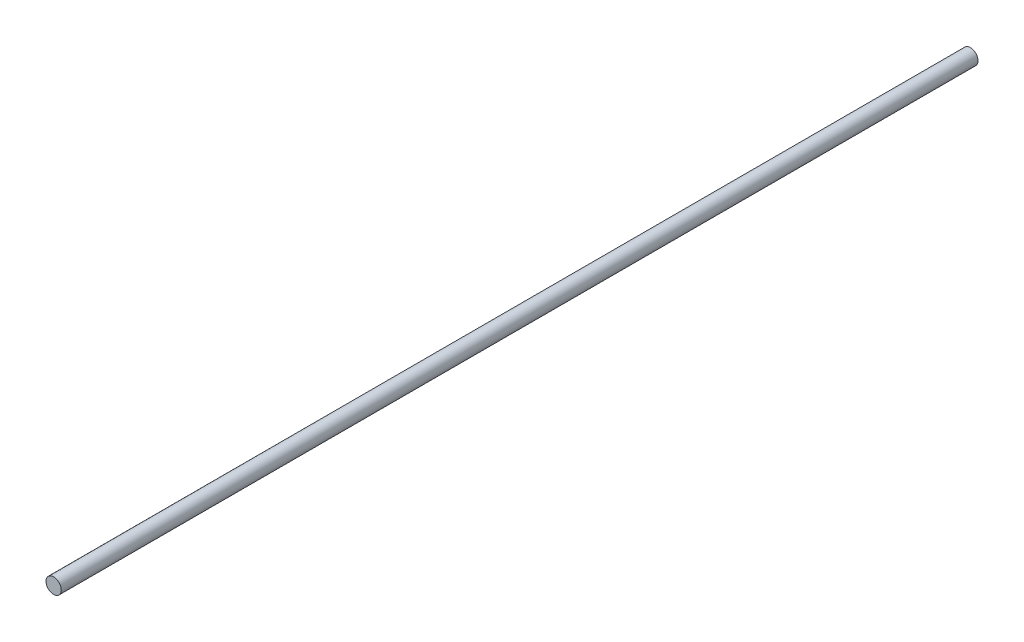
SolidWorks part; units mm, degrees
ref_plane "Plano frontal" through (0, 0, 0) normal (0, 0, 1) x (1, 0, 0)
ref_plane "Plano superior" through (0, 0, 0) normal (0, 1, 0) x (1, 0, 0)
ref_plane "Plano direito" through (0, 0, 0) normal (1, 0, 0) x (0, 0, -1)
sketch "Esboço1" plane through (0, 0, 0) normal (0, 0, 1) x (1, 0, 0)
  circle A0 centre (0, 0) radius 2.5
  dimension "D1" = 5
extrude "Ressalto-extrusão1" add sketch "Esboço1" along normal mid plane 300
